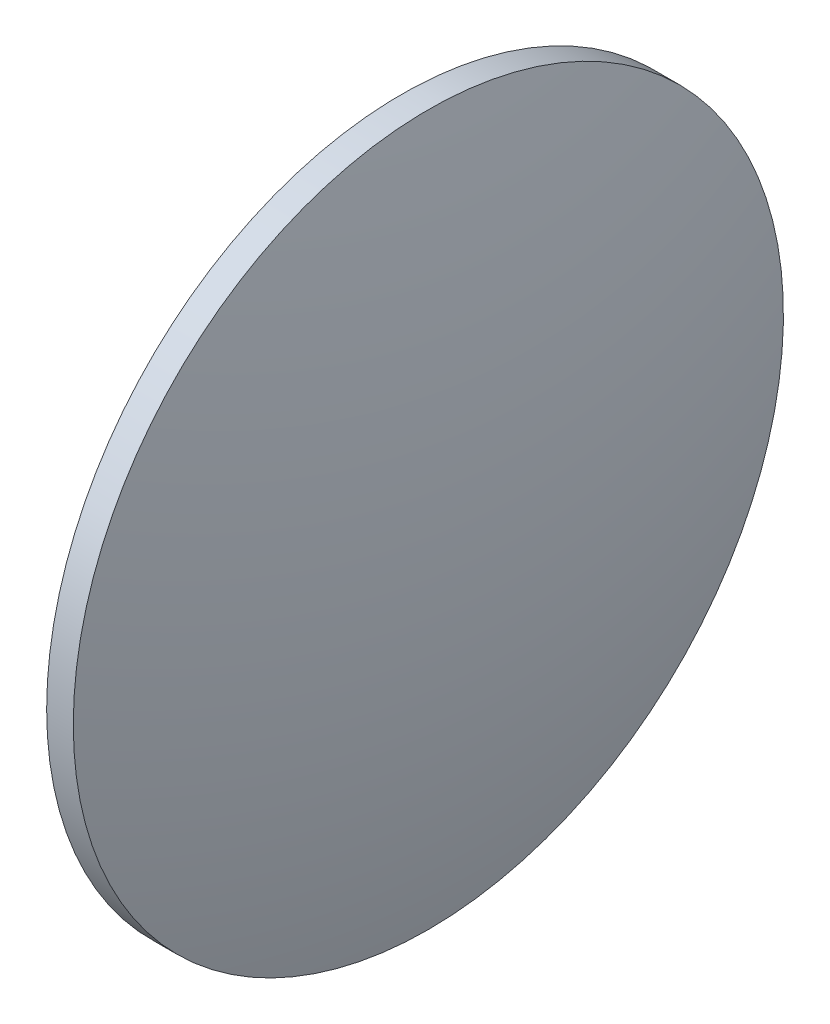
SolidWorks part; units mm, degrees
ref_plane "前视基准面" through (0, 0, 0) normal (0, 0, 1) x (1, 0, 0)
ref_plane "上视基准面" through (0, 0, 0) normal (0, 1, 0) x (1, 0, 0)
ref_plane "右视基准面" through (0, 0, 0) normal (1, 0, 0) x (0, 0, -1)
sketch "草图1" plane through (0, 0, 0) normal (0, 0, 1) x (1, 0, 0)
  line L0 (767.9519, 121.1916) -> (821.7348, 121.1916) construction
  line L1 (786.7768, 121.1916) -> (786.7768, 161.1916)
  line L2 (795.027, 121.1916) -> (786.7768, 121.1916)
  line L5 (789.7768, 161.1916) -> (786.7768, 161.1916)
  arc A0 (795.027, 121.1916) -> (789.7768, 161.1916) centre (640.0263, 121.1916) ccw
revolve "旋转1" add sketch "草图1" angle 360 about L0
